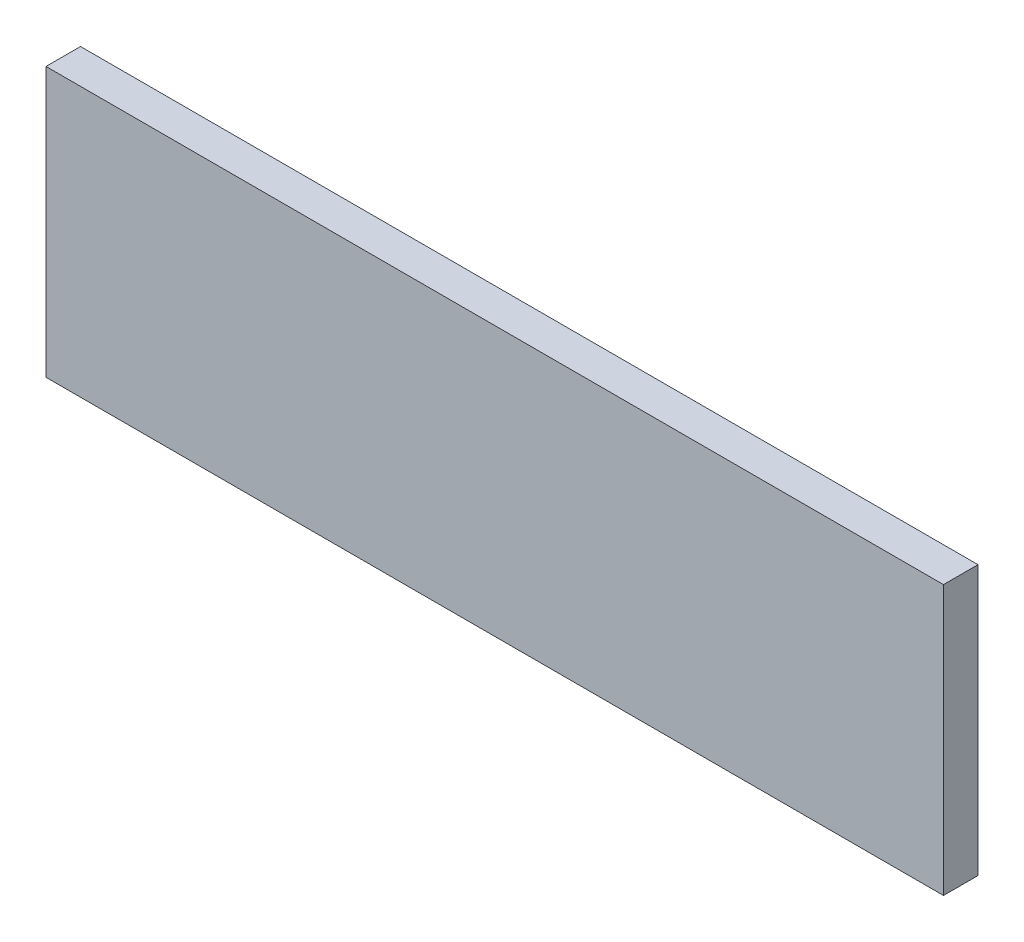
SolidWorks part; units mm, degrees
ref_plane "Front Plane" through (0, 0, 0) normal (0, 0, 1) x (1, 0, 0)
ref_plane "Top Plane" through (0, 0, 0) normal (0, 1, 0) x (1, 0, 0)
ref_plane "Right Plane" through (0, 0, 0) normal (1, 0, 0) x (0, 0, -1)
sketch "Sketch1" plane through (0, 0, 0) normal (0, 0, 1) x (1, 0, 0)
  line L1 (0, 0) -> (33.02, 0)
  line L2 (0, 0) -> (0, 9.906)
  line L3 (0, 9.906) -> (33.02, 9.906)
  line L4 (33.02, 0) -> (33.02, 9.906)
  dimension "D1" = 9.906
  dimension "D2" = 33.02
extrude "Boss-Extrude1" add sketch "Sketch1" along normal blind 1.27
